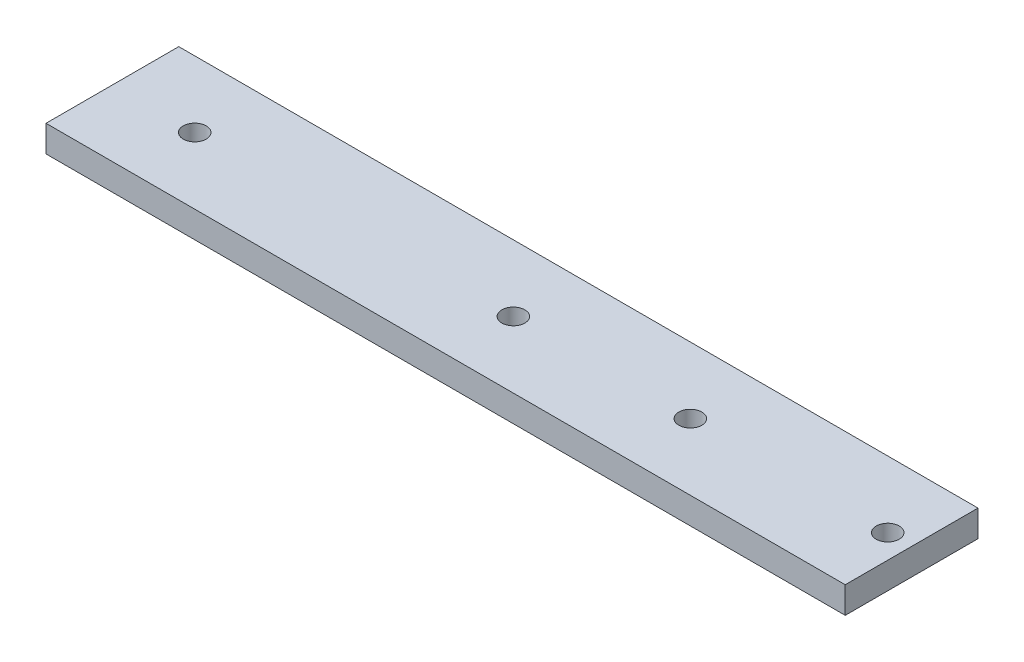
SolidWorks part; units mm, degrees
ref_plane "前视基准面" through (0, 0, 0) normal (0, 0, 1) x (1, 0, 0)
ref_plane "上视基准面" through (0, 0, 0) normal (0, 1, 0) x (1, 0, 0)
ref_plane "右视基准面" through (0, 0, 0) normal (1, 0, 0) x (0, 0, -1)
sketch "草图1" plane through (0, 0, 0) normal (0, 1, 0) x (1, 0, 0)
  line L0 (-65.3034, 7.5) -> (-65.3034, -7.5)
  line L1 (0, 7.5) -> (25, 7.5)
  line L2 (25, 7.5) -> (25, 0)
  line L3 (25, -7.5) -> (0, -7.5)
  line L4 (0, -7.5) -> (-20, -7.5)
  line L5 (-20, -7.5) -> (-56, -7.5)
  line L6 (-56, -7.5) -> (-65.3034, -7.5)
  line L7 (25, 0) -> (25, -7.5)
  line L8 (-65.3034, 7.5) -> (0, 7.5)
  line L9 (-56, -7.5) -> (-56, 0) construction
  line L10 (-56, 0) -> (-20, 0) construction
  line L11 (0, 0) -> (22.3, 0) construction
  circle A0 centre (-56, 0) radius 1.3
  circle A1 centre (-20, 0) radius 1.3
  circle A2 centre (0, 0) radius 1.3
  circle A3 centre (22.3, 0) radius 1.3
extrude "凸台-拉伸1" add sketch "草图1" along normal blind 3
